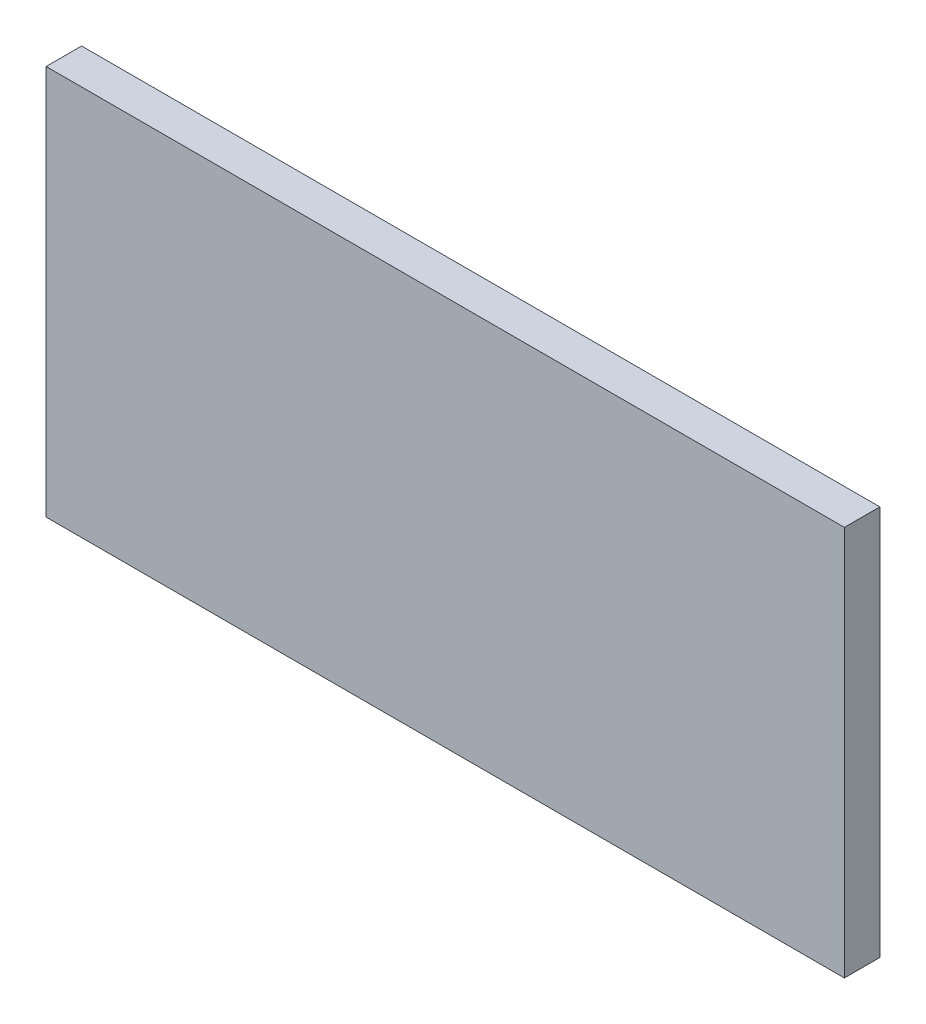
SolidWorks part; units mm, degrees
ref_plane "正面" through (0, 0, 0) normal (0, 0, 1) x (1, 0, 0)
ref_plane "平面" through (0, 0, 0) normal (0, 1, 0) x (1, 0, 0)
ref_plane "右側面" through (0, 0, 0) normal (1, 0, 0) x (0, 0, -1)
sketch "ｽｹｯﾁ1" plane through (0, 0, 0) normal (0, 0, 1) x (1, 0, 0)
  line L1 (-38.2975, 23.2366) -> (51.7025, 23.2366)
  line L2 (-38.2975, 23.2366) -> (-38.2975, -20.7634)
  line L3 (-38.2975, -20.7634) -> (51.7025, -20.7634)
  line L4 (51.7025, 23.2366) -> (51.7025, -20.7634)
  dimension "D1" = 44
extrude "ﾎﾞｽ - 押し出し1" add sketch "ｽｹｯﾁ1" along normal blind 4
